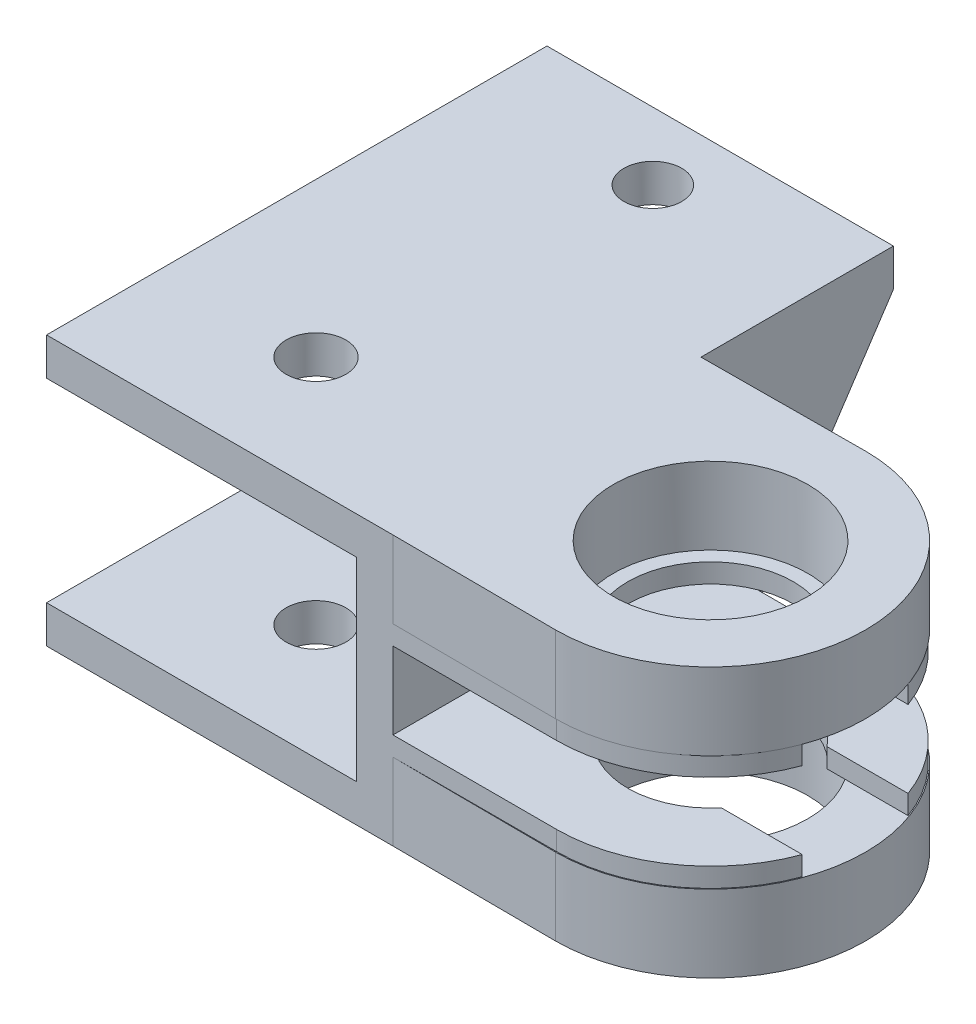
SolidWorks part; units mm, degrees
material "Resin - ARL printer"
ref_plane "Front Plane" through (0, 0, 0) normal (0, 0, 1) x (1, 0, 0)
ref_plane "Top Plane" through (0, 0, 0) normal (0, 1, 0) x (1, 0, 0)
ref_plane "Right Plane" through (0, 0, 0) normal (1, 0, 0) x (0, 0, -1)
sketch "Sketch1" plane through (0, 0, 0) normal (0, 1, 0) x (1, 0, 0)
  line L0 (0, 0) -> (0, 30319.3642) construction
  line L1 (-18, 8) -> (0, 8)
  line L2 (-18, 8) -> (-18, -8)
  line L3 (-18, -8) -> (0, -8)
  line L4 (0, 8) -> (0, -8)
  line L5 (0, 0) -> (30319.3642, 0) construction
  point P11 (0, -8)
  dimension "D1" = 18
  dimension "D2" = 16
extrude "Boss-Extrude1" add sketch "Sketch1" along normal mid plane 14
ref_plane "Plane1" through (0, 0, 0) normal (0, -1, 0) x (-1, 0, 0)
sketch "Sketch4" plane through (-18, 0, 0) normal (-1, 0, 0) x (0, 0, 1)
  line L0 (-8, 7) -> (-8, -7) construction
  line L1 (-8, -5.05) -> (8, -5.05)
  line L2 (-8, -5.05) -> (-8, 5.05)
  line L3 (-8, 5.05) -> (8, 5.05)
  line L4 (8, -5.05) -> (8, 5.05)
  line L5 (8, 7) -> (8, -7) construction
  line L6 (0, 0) -> (50000, 0) construction
  dimension "D1" = 10.1
extrude "Cut-Extrude1" cut sketch "Sketch4" against normal blind 16.1
sketch "Sketch5" plane through (0, -7, 0) normal (0, -1, 0) x (1, 0, 0)
  line L0 (0, 0) -> (50000, 0) construction
  line L1 (0, 8) -> (8.5, 8.05)
  line L2 (0, 8) -> (0, -8)
  line L3 (0, -8) -> (8.5, -8.05)
  circle A0 centre (8.5, 0) radius 5.05
  circle A1 centre (8.5, 0) radius 8.05 construction
  arc A2 (8.5, -8.05) -> (8.5, 8.05) centre (8.5, 0) ccw
  dimension "D1" = 10.1
  dimension "D2" = 3
  dimension "D3" = 8.5
extrude "Boss-Extrude2" add sketch "Sketch5" against normal blind 4
mirror "Mirror1" about plane through (0, 0, 0) normal (0, -1, 0) of "Boss-Extrude2"
sketch "Sketch7" plane through (0, 0, -8) normal (0, 0, -1) x (-1, 0, 0)
  line L0 (0, 7) -> (18, 7) construction
  line L5 (-16.55, 7) -> (-16.55, 3) construction
  line L7 (0, 5.05) -> (18, 5.05)
  line L8 (0, 5.05) -> (0, 7)
  line L9 (0, 7) -> (18, 7)
  line L10 (18, 5.05) -> (18, 7)
  line L11 (0, 3) -> (0, -3) construction
  point P6 (-16.55, 5)
  point P7 (18, -7)
extrude "Boss-Extrude3" add sketch "Sketch7" along normal blind 10
sketch "Sketch8" plane through (0, 7, 0) normal (0, -1, 0) x (1, 0, 0)
  line L0 (-18, -8) -> (0, -8) construction
  line L1 (-9, -8) -> (-9, -18) construction
  line L2 (0, -18) -> (-18, -18) construction
  line L3 (0, -8) -> (-18, -8) construction
  circle A0 centre (-9, -14.5) radius 1.5
  dimension "D1" = 3
  dimension "D2" = 3.5
extrude "Cut-Extrude2" cut sketch "Sketch8" along normal up to surface (1.95 mm away) up to face at (-6.6333, 5.05, -6)
sketch "Sketch9" plane through (0, -3, 0) normal (0, 1, 0) x (1, 0, 0)
  line L0 (11.8057, -2.75) -> (16.0125, -2.75)
  line L1 (11.8057, 2.75) -> (16.0125, 2.75)
  line L2 (0, 0) -> (50000, 0) construction
  line L3 (8.5, -8) -> (0, -8)
  line L4 (0, -8) -> (0, 8)
  line L5 (0, 8) -> (8.5, 8)
  circle A0 centre (8.5, 0) radius 4.3 construction
  circle A1 centre (8.5, 0) radius 8 construction
  arc A4 (11.8057, -2.75) -> (11.8057, 2.75) centre (8.5, 0) cw
  arc A5 (16.0125, -2.75) -> (8.5, -8) centre (8.5, 0) cw
  arc A6 (16.0125, 2.75) -> (8.5, 8) centre (8.5, 0) ccw
  dimension "D1" = 8.6
  dimension "D2" = 5.5
extrude "Boss-Extrude4" add sketch "Sketch9" along normal blind 1
mirror "Mirror2" about plane through (0, 0, 0) normal (0, -1, 0) of "Boss-Extrude4"
sketch "Sketch10" plane through (0, -7, 0) normal (0, -1, 0) x (1, 0, 0)
  circle A1 centre (-10, 2) radius 1.55
  circle A3 centre (-10, 2) radius 1.55 construction
extrude "Cut-Extrude3" cut sketch "Sketch10" against normal up to surface (14 mm away)
sketch "Sketch13" plane through (0, 0, -8) normal (0, 0, -1) x (-1, 0, 0)
  line L1 (0, 5.05) -> (18, 5.05)
  line L2 (0, 5.05) -> (0, -7)
  line L3 (0, -7) -> (18, -7)
  line L4 (18, 5.05) -> (18, -7)
extrude "Boss-Extrude6" add sketch "Sketch13" along normal blind 2
sketch "Sketch14" plane through (0, 0, 0) normal (1, 0, 0) x (0, 0, -1)
  line L0 (10, -7) -> (18, 5.05)
  line L1 (18, 5.05) -> (10, 5.05)
  line L2 (10, 5.05) -> (10, -7)
extrude "Boss-Extrude7" add sketch "Sketch14" against normal blind 2
ref_plane "Plane2" through (-9, 0, 0) normal (1, 0, 0) x (0, 0, -1)
mirror "Mirror3" about plane through (-9, 0, 0) normal (1, 0, 0) of "Boss-Extrude7"
sketch "Sketch15" plane through (0, 0, -8) normal (0, 0, 1) x (1, 0, 0)
  line L1 (-18, 5.05) -> (-1.9, 5.05)
  line L2 (-18, 5.05) -> (-18, -5.05)
  line L3 (-18, -5.05) -> (-1.9, -5.05)
  line L4 (-1.9, 5.05) -> (-1.9, -5.05)
extrude "Cut-Extrude4" cut sketch "Sketch15" against normal blind 0.1
